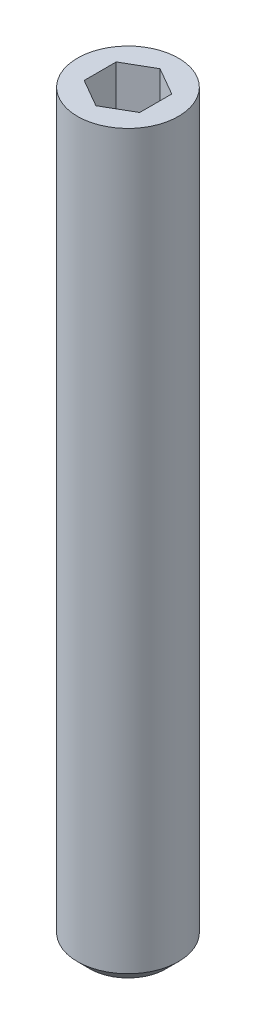
SolidWorks part; units mm, degrees
ref_plane "Front Plane" through (0, 0, 0) normal (0, 0, 1) x (1, 0, 0)
ref_plane "Top Plane" through (0, 0, 0) normal (0, 1, 0) x (1, 0, 0)
ref_plane "Right Plane" through (0, 0, 0) normal (1, 0, 0) x (0, 0, -1)
sketch "Sketch1" plane through (0, 0, 0) normal (0, 1, 0) x (1, 0, 0)
  circle A0 centre (0, 0) radius 2
  dimension "D1" = 4
extrude "Boss-Extrude1" add sketch "Sketch1" along normal blind 29.5
chamfer "Chamfer1" distance 0.5 angle 45 1 edges at (0, 0, 2)
sketch "Sketch2" plane through (0, 29.5, 0) normal (0, 1, 0) x (1, 0, 0)
  line L1 (1.1, 0.6351) -> (0, 1.2702)
  line L2 (0, 1.2702) -> (-1.1, 0.6351)
  line L3 (-1.1, 0.6351) -> (-1.1, -0.6351)
  line L4 (-1.1, -0.6351) -> (0, -1.2702)
  line L5 (0, -1.2702) -> (1.1, -0.6351)
  line L6 (1.1, -0.6351) -> (1.1, 0.6351)
  circle A0 centre (0, 0) radius 1.1 construction
  dimension "D1" = 2.2
extrude "Cut-Extrude1" cut sketch "Sketch2" against normal blind 2
